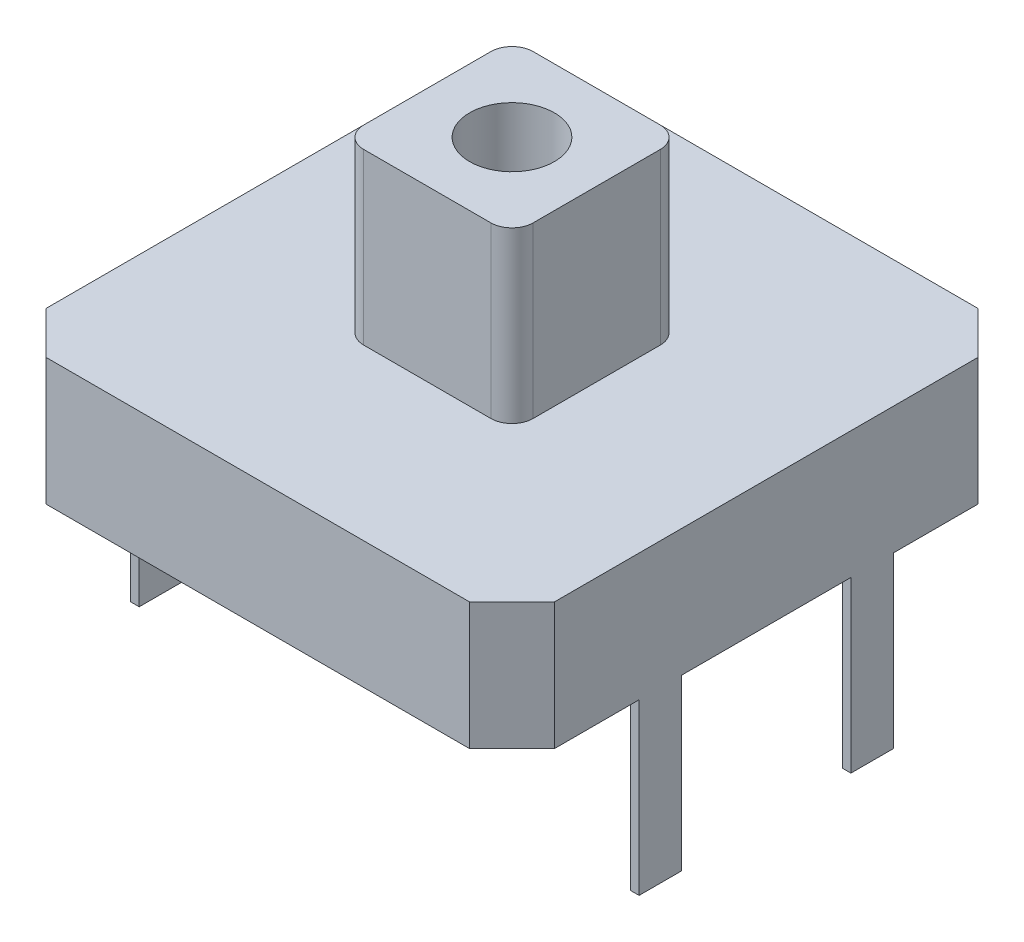
SolidWorks part; units mm, degrees
ref_plane "Front Plane" through (0, 0, 0) normal (0, 0, 1) x (1, 0, 0)
ref_plane "Top Plane" through (0, 0, 0) normal (0, 1, 0) x (1, 0, 0)
ref_plane "Right Plane" through (0, 0, 0) normal (1, 0, 0) x (0, 0, -1)
sketch "Sketch1" plane through (0, 0, 0) normal (0, 1, 0) x (1, 0, 0)
  line L1 (-6, -6) -> (6, -6)
  line L2 (-6, -6) -> (-6, 6)
  line L3 (-6, 6) -> (6, 6)
  line L4 (6, -6) -> (6, 6)
  line L5 (-6, -6) -> (6, 6) construction
  line L6 (-6, 6) -> (6, -6) construction
  point P0 (0, 0)
  dimension "D1" = 12
extrude "Boss-Extrude1" add sketch "Sketch1" along normal blind 3
sketch "Sketch2" plane through (0, 3, 0) normal (0, 1, 0) x (1, 0, 0)
  line L1 (-2, -2) -> (2, -2)
  line L2 (-2, -2) -> (-2, 2)
  line L3 (-2, 2) -> (2, 2)
  line L4 (2, -2) -> (2, 2)
  line L5 (-2, -2) -> (2, 2) construction
  line L6 (-2, 2) -> (2, -2) construction
  point P0 (0, 0)
  dimension "D1" = 4
extrude "Boss-Extrude2" add sketch "Sketch2" along normal blind 4
sketch "Sketch3" plane through (0, 7, 0) normal (0, 1, 0) x (1, 0, 0)
  circle A0 centre (0, 0) radius 1
  dimension "D1" = 2
extrude "Cut-Extrude1" cut sketch "Sketch3" against normal blind 3
fillet "Fillet2" radius 0.5 4 edges at (2, 5, -2) (-2, 5, -2) (-2, 5, 2) (2, 5, 2)
sketch "Sketch4" plane through (0, 0, 0) normal (0, -1, 0) x (1, 0, 0)
  line L0 (-6, 0) -> (6, 0) construction
  line L3 (-6, -6) -> (-6, 6) construction
  line L4 (6, 6) -> (6, -6) construction
  line L5 (0, 6) -> (0, -6) construction
  line L6 (-6, 6) -> (6, 6) construction
  line L7 (6, -6) -> (-6, -6) construction
  line L8 (-6, -3) -> (-5.8, -3)
  line L9 (-6, 2) -> (-5.8, 2)
  line L10 (-6, 2) -> (-6, 3)
  line L11 (-6, 3) -> (-5.8, 3)
  line L12 (-5.8, 2) -> (-5.8, 3)
  line L13 (-6, 2) -> (-5.8, 3) construction
  line L14 (-6, 3) -> (-5.8, 2) construction
  line L15 (-5.8, -2) -> (-5.8, -3)
  line L16 (-6, -2) -> (-5.8, -2)
  line L17 (-6, -2) -> (-6, -3)
  line L18 (6, 3) -> (5.8, 3)
  line L19 (5.8, 2) -> (5.8, 3)
  line L20 (6, 2) -> (5.8, 2)
  line L21 (6, 2) -> (6, 3)
  line L22 (6, -2) -> (6, -3)
  line L23 (6, -2) -> (5.8, -2)
  line L24 (5.8, -2) -> (5.8, -3)
  line L25 (6, -3) -> (5.8, -3)
  point P12 (-5.9, 2.5)
  dimension "D1" = 3
  dimension "D2" = 0.2
  dimension "D3" = 1
extrude "Boss-Extrude3" add sketch "Sketch4" along normal blind 4
chamfer "Chamfer1" distance 1 angle 45 4 edges at (-6, 1.5, 6) (6, 1.5, 6) (-6, 1.5, -6) (6, 1.5, -6)
